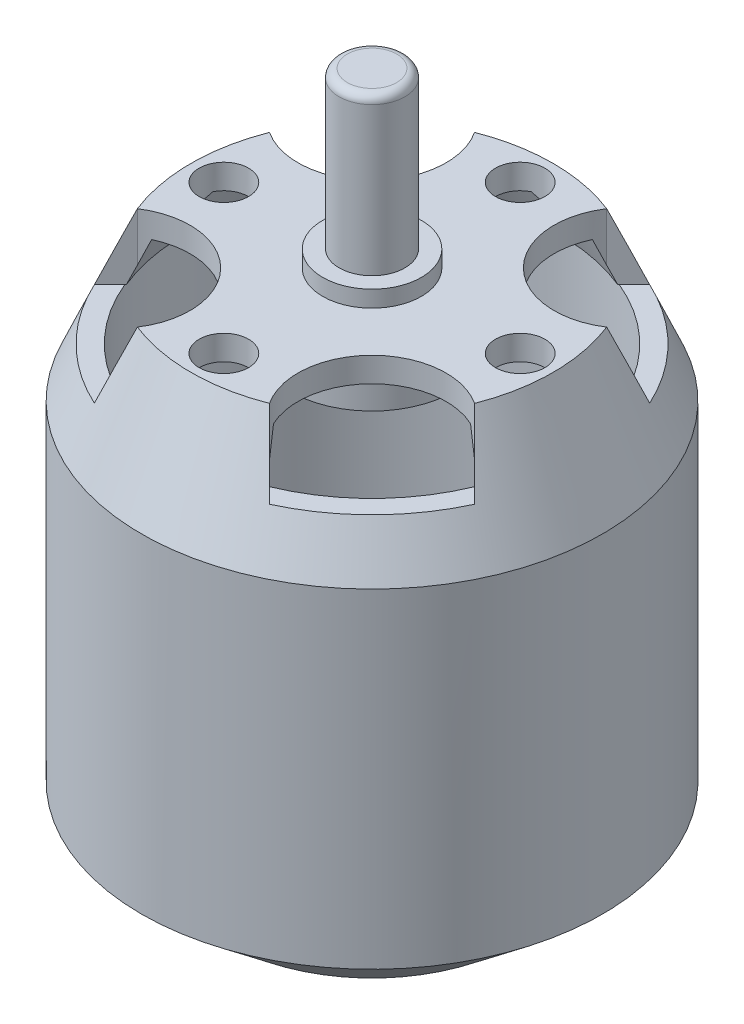
SolidWorks part; units mm, degrees
ref_plane "Front Plane" through (0, 0, 0) normal (0, 0, 1) x (1, 0, 0)
ref_plane "Top Plane" through (0, 0, 0) normal (0, 1, 0) x (1, 0, 0)
ref_plane "Right Plane" through (0, 0, 0) normal (1, 0, 0) x (0, 0, -1)
sketch "Sketch1" plane through (0, 0, 0) normal (0, 1, 0) x (1, 0, 0)
  circle A0 centre (0, 0) radius 14
  dimension "D1" = 28
extrude "Boss-Extrude1" add sketch "Sketch1" along normal blind 18
ref_plane "Plane1" through (0, 25, 0) normal (0, 1, 0) x (1, 0, 0)
sketch "Sketch2" plane through (0, 25, 0) normal (0, 1, 0) x (1, 0, 0)
  circle A0 centre (0, 0) radius 11
  dimension "D1" = 22
loft "Loft1" add profiles "Sketch2" section "Sketch2" section face at (0, 18, 14)
sketch "Sketch3" plane through (0, 25, 0) normal (0, 1, 0) x (1, 0, 0)
  circle A0 centre (0, 0) radius 3
  circle A1 centre (0, 0) radius 1.5
  dimension "D1" = 6
  dimension "D2" = 3
extrude "Boss-Extrude2" add sketch "Sketch3" along normal blind 1
sketch "Sketch4" plane through (0, 25, 0) normal (0, 1, 0) x (1, 0, 0)
  circle A0 centre (0, 0) radius 2
  dimension "D1" = 4
extrude "Boss-Extrude3" add sketch "Sketch4" along normal blind 10.5
sketch "Sketch7" plane through (0, 0, 0) normal (0, -1, 0) x (1, 0, 0)
  circle A0 centre (0, 0) radius 14
extrude "Boss-Extrude5" add sketch "Sketch7" along normal blind 2
ref_plane "Plane2" through (0, -6, 0) normal (0, -1, 0) x (-1, 0, 0)
sketch "Sketch5" plane through (0, -6, 0) normal (0, -1, 0) x (-1, 0, 0)
  circle A0 centre (0, 0) radius 9
  dimension "D1" = 18
loft "Loft2" add profiles "Sketch5" section "Sketch5" section face at (0, -2, -14)
sketch "Sketch6" plane through (0, -6, 0) normal (0, -1, 0) x (1, 0, 0)
  circle A0 centre (0, 0) radius 4.5
  dimension "D1" = 9
extrude "Boss-Extrude4" add sketch "Sketch6" along normal blind 2
sketch "Sketch9" plane through (0, 25, 0) normal (0, 1, 0) x (1, 0, 0)
  circle A0 centre (0, 9) radius 1.5
  circle A1 centre (9, 0) radius 1.5
  circle A2 centre (0, -9) radius 1.5
  circle A3 centre (-9, 0) radius 1.5
  point P12 (0, 0)
  dimension "D1" = 3
  dimension "D2" = 9
  dimension "D3" = 4
extrude "Cut-Extrude5" cut sketch "Sketch9" against normal blind 4
sketch "Sketch10" plane through (0, -6, 0) normal (0, -1, 0) x (1, 0, 0)
  circle A0 centre (0, 9) radius 1.5
  circle A1 centre (0, 0) radius 9 construction
  circle A2 centre (9, 0) radius 1.5
  circle A3 centre (0, -9) radius 1.5
  circle A4 centre (-9, 0) radius 1.5
  point P14 (0, 0)
  dimension "D1" = 3
  dimension "D2" = 4
extrude "Cut-Extrude6" cut sketch "Sketch10" against normal blind 4
sketch "Sketch11" plane through (0, -6, 0) normal (0, -1, 0) x (1, 0, 0)
  circle A0 centre (0, 6) radius 1
  circle A1 centre (6, 0) radius 1
  circle A2 centre (0, -6) radius 1
  circle A3 centre (-6, 0) radius 1
  point P0 (0, 9)
  point P14 (0, 0)
  dimension "D2" = 2
  dimension "D1" = 3
  dimension "D3" = 4
extrude "Cut-Extrude7" cut sketch "Sketch11" against normal blind 2
sketch "Sketch12" plane through (0, 25, 0) normal (0, 1, 0) x (1, 0, 0)
  line L0 (0, 0) -> (-7.7782, -7.7782) construction
  line L1 (-7.7782, -7.7782) -> (7.7782, -7.7782) construction
  line L2 (-10.242, -4.0126) -> (-4.0126, -10.242) construction
  line L3 (-10.242, -4.0126) -> (-13.0142, -6.7848)
  line L4 (-13.0142, -6.7848) -> (-6.7848, -13.0142)
  line L5 (-6.7848, -13.0142) -> (-4.0126, -10.242)
  line L6 (-13.0142, 6.7848) -> (-10.242, 4.0126)
  line L7 (-6.7848, 13.0142) -> (-13.0142, 6.7848)
  line L8 (-4.0126, 10.242) -> (-6.7848, 13.0142)
  line L9 (6.7848, 13.0142) -> (4.0126, 10.242)
  line L10 (13.0142, 6.7848) -> (6.7848, 13.0142)
  line L11 (10.242, 4.0126) -> (13.0142, 6.7848)
  line L12 (13.0142, -6.7848) -> (10.242, -4.0126)
  line L13 (6.7848, -13.0142) -> (13.0142, -6.7848)
  line L14 (4.0126, -10.242) -> (6.7848, -13.0142)
  circle A0 centre (0, 0) radius 11 construction
  arc A1 (-10.242, -4.0126) -> (-4.0126, -10.242) centre (-7.7782, -7.7782) cw
  arc A2 (-4.0126, 10.242) -> (-10.242, 4.0126) centre (-7.7782, 7.7782) cw
  arc A3 (10.242, 4.0126) -> (4.0126, 10.242) centre (7.7782, 7.7782) cw
  arc A4 (4.0126, -10.242) -> (10.242, -4.0126) centre (7.7782, -7.7782) cw
  circle A5 centre (0, 0) radius 14 construction
  point P28 (0, 0)
  dimension "D1" = 45
  dimension "D2" = 4.5
  dimension "D4" = 4
extrude "Cut-Extrude8" cut sketch "Sketch12" against normal blind 4
sketch "Sketch13" plane through (0, 21, 0) normal (0, 1, 0) x (1, 0, 0)
  circle A0 centre (0, 0) radius 11.5
  circle A1 centre (0, 0) radius 14 construction
  dimension "D1" = 2.5
extrude "Cut-Extrude9" cut sketch "Sketch13" against normal blind 22.5
fillet "Fillet1" radius 0.5 2 edges at (0, 35.5, 2) (0, -8, -4.5)
sketch "Sketch17" plane through (0, 0, 0) normal (0, 0, 1) x (1, 0, 0)
  line L0 (-10.3681, 23.5) -> (-11.4396, 21)
  line L1 (-11, 25) -> (-12.6657, 21.1135) construction
  line L3 (-11, 25) -> (-14, 18) construction
  line L4 (-10.3681, 23.5) -> (-5, 23.5)
  line L5 (-5, 23.5) -> (-5, 21)
  line L6 (-5, 21) -> (-11.4396, 21)
  line L7 (0, 25) -> (0, 21.1135) construction
  line L8 (4.0126, 25) -> (-4.0126, 25) construction
  line L11 (-3.2782, 25) -> (-10.242, 25) construction
  line L12 (-10.242, 21) -> (-3.2782, 21) construction
  dimension "D2" = 1.5
  dimension "D3" = 5
  dimension "D4" = 2.3433
revolve "Cut-Revolve1" cut sketch "Sketch17" angle 360 about L7
